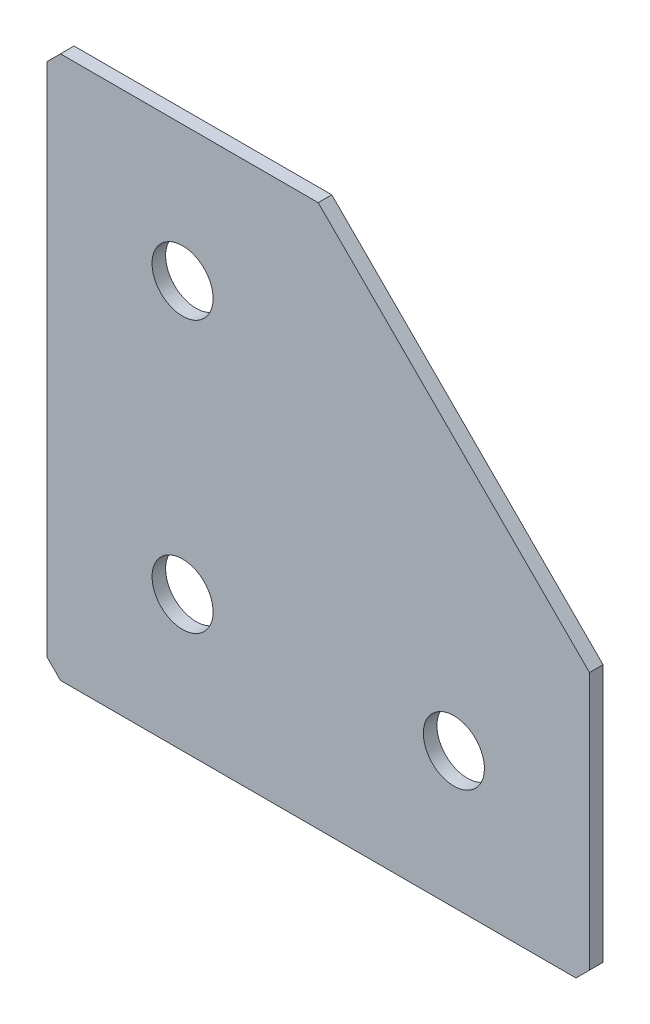
SolidWorks part; units mm, degrees
material "Простая углеродистая сталь"
ref_plane "Спереди(Плоскость XY)" through (0, 0, 0) normal (0, 0, 1) x (1, 0, 0)
ref_plane "Сверху(Плоскость XZ)" through (0, 0, 0) normal (0, 1, 0) x (1, 0, 0)
ref_plane "Справа(Плоскость ZY)" through (0, 0, 0) normal (1, 0, 0) x (0, 0, -1)
sketch "Эскиз1" plane through (0, 0, 0) normal (0, 0, -1) x (1, 0, 0)
  line L0 (0, 0) -> (0, 80)
  line L1 (0, 80) -> (80, 80)
  line L2 (80, 80) -> (80, 40)
  line L3 (80, 40) -> (40, 40) construction
  line L4 (40, 40) -> (40, 0) construction
  line L5 (40, 0) -> (0, 0)
  line L6 (80, 40) -> (40, 0)
  dimension "D1" = 80
  dimension "D2" = 40
  dimension "D3" = 40
  dimension "D4" = 40
extrude "Бобышка-Вытянуть1" add sketch "Эскиз1" along normal blind 2
hole_wizard "Отверстие с зазором M81" positions "Эскиз2" profile "Эскиз3" hole size "M8" standard "DIN" end condition through all
sketch "Эскиз2" plane through (0, 0, -2) normal (0, 0, -1) x (1, 0, 0)
  line L1 (0, 0) -> (40, 0) construction
  line L6 (0, 80) -> (0, 0) construction
  point P4 (20, 60)
  point P6 (20, 20)
  point P29 (60, 60)
  dimension "D1" = 40
  dimension "D2" = 40
  dimension "D4" = 20
  dimension "D5" = 20
sketch "Эскиз3" plane through (20, -60, -2) normal (1, 0, 0) x (0, 1, 0)
  line L0 (0, 0) -> (0, 2)
  line L1 (0, 2) -> (4.5, 2)
  line L2 (4.5, 2) -> (4.5, 0)
  line L5 (4.5, 0) -> (0, 0)
  line L11 (0, -6.35) -> (0, 107.95) construction
  dimension "Диаметр сквозного отверстия" = 9
  dimension "Глубина сквозного отверстия" = 2
chamfer "Фаска1" distance 2 angle 45 3 edges at (0, 0, -1) (80, -80, -1) (0, -80, -1)
